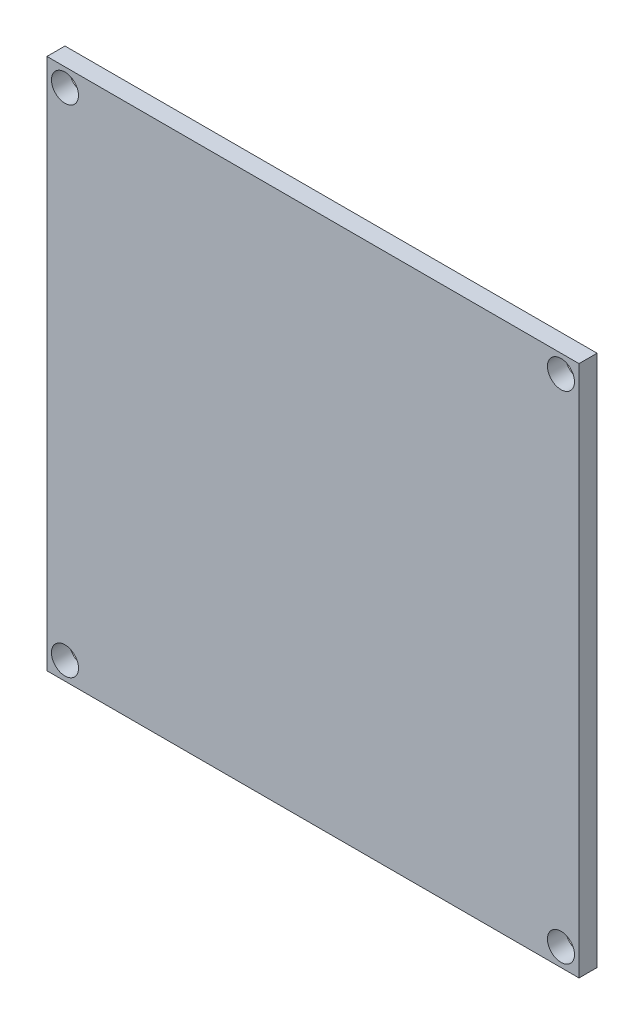
SolidWorks part; units mm, degrees
ref_plane "Alzado" through (0, 0, 0) normal (0, 0, 1) x (1, 0, 0)
ref_plane "Planta" through (0, 0, 0) normal (0, 1, 0) x (1, 0, 0)
ref_plane "Vista lateral" through (0, 0, 0) normal (1, 0, 0) x (0, 0, -1)
sketch "Croquis1" plane through (0, 0, 0) normal (0, 0, 1) x (1, 0, 0)
  line L1 (-89.1419, 30.4888) -> (-30.1419, 30.4888)
  line L2 (-89.1419, 30.4888) -> (-89.1419, -28.5112)
  line L3 (-89.1419, -28.5112) -> (-30.1419, -28.5112)
  line L4 (-30.1419, 30.4888) -> (-30.1419, -28.5112)
  circle A0 centre (-87.1419, 28.4888) radius 1.5
  circle A1 centre (-32.1419, 28.4888) radius 1.5
  circle A2 centre (-32.1419, -26.5112) radius 1.5
  circle A3 centre (-87.1419, -26.5112) radius 1.5
  dimension "D3" = 2
  dimension "D1" = 59
  dimension "D2" = 59
  dimension "D4" = 2
  dimension "D5" = 2
  dimension "D6" = 2
extrude "Saliente-Extruir3" add sketch "Croquis1" along normal blind 2
